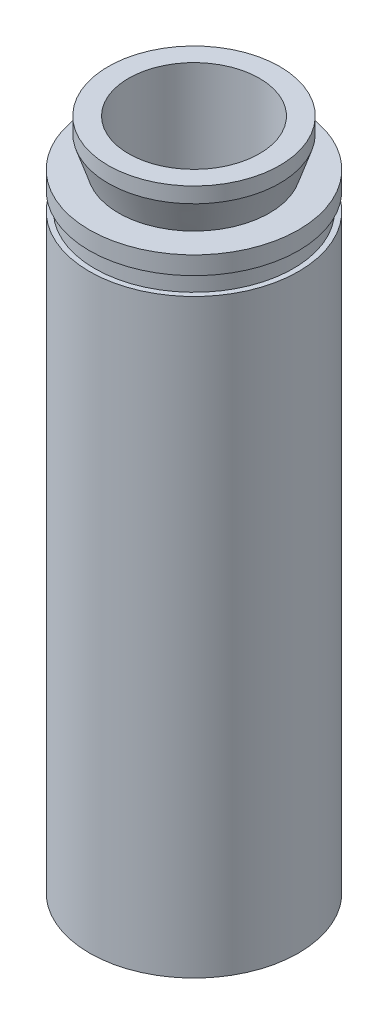
SolidWorks part; units mm, degrees
ref_plane "Front Plane" through (0, 0, 0) normal (0, 0, 1) x (1, 0, 0)
ref_plane "Top Plane" through (0, 0, 0) normal (0, 1, 0) x (1, 0, 0)
ref_plane "Right Plane" through (0, 0, 0) normal (1, 0, 0) x (0, 0, -1)
sketch "Sketch1" plane through (0, 0, 0) normal (0, 0, 1) x (1, 0, 0)
  line L0 (-17.45, 0) -> (-20.3, 0)
  line L1 (-20.3, 0) -> (-20.3, 114.6)
  line L2 (-20.3, 118.1) -> (-19.3, 118.1)
  line L3 (-19.3, 118.1) -> (-19.3, 114.6)
  line L4 (-19.3, 114.6) -> (-20.3, 114.6)
  line L5 (-20.3, 118.1) -> (-20.3, 121.6)
  line L6 (-20.3, 121.6) -> (-14.65, 121.6)
  line L7 (-14.65, 121.6) -> (-16.65, 127.6)
  line L8 (-16.65, 127.6) -> (-16.65, 130.6)
  line L9 (-16.65, 130.6) -> (-12.7, 130.6)
  line L11 (-12.7, 130.6) -> (-12.7, 111.6)
  line L14 (0, 0) -> (0, 152.5934) construction
  line L15 (-17.45, 0) -> (-17.45, 111.6)
  line L16 (-17.45, 111.6) -> (-12.7, 111.6)
  dimension "D2" = 121.6
  dimension "D3" = 130.6
  dimension "D4" = 3
  dimension "D6" = 20.3
  dimension "D7" = 3.5
  dimension "D8" = 3.5
  dimension "D9" = 1
  dimension "D10" = 130.6
  dimension "D11" = 3.65
  dimension "D12" = 6.6
  dimension "D13" = 5.65
  dimension "D14" = 3
  dimension "D15" = 3.95
  dimension "D16" = 17.45
  dimension "D17" = 10
  dimension "D18" = 12.7
revolve "Revolve1" add sketch "Sketch1" angle 360 about L14
